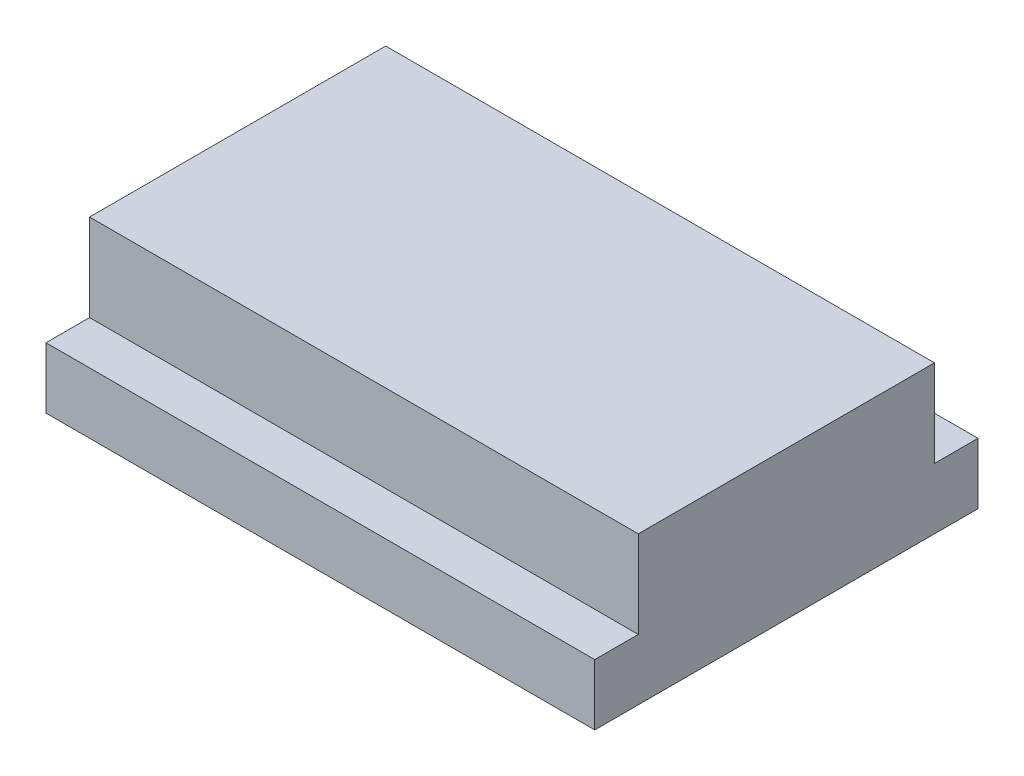
SolidWorks part; units mm, degrees
material "ABS"
ref_plane "Front" through (0, 0, 0) normal (0, 0, 1) x (1, 0, 0)
ref_plane "Top" through (0, 0, 0) normal (0, 1, 0) x (1, 0, 0)
ref_plane "Right" through (0, 0, 0) normal (1, 0, 0) x (0, 0, -1)
sketch "Sketch1" plane through (0, 0, 0) normal (0, 1, 0) x (1, 0, 0)
  line L1 (-31.5, 22) -> (31.5, 22)
  line L2 (-31.5, 22) -> (-31.5, -22)
  line L3 (-31.5, -22) -> (31.5, -22)
  line L4 (31.5, 22) -> (31.5, -22)
  line L5 (-31.5, 22) -> (31.5, -22) construction
  line L6 (-31.5, -22) -> (31.5, 22) construction
  point P0 (0, 0)
  dimension "D1" = 63
  dimension "D2" = 44
extrude "Boss-Extrude1" add sketch "Sketch1" along normal blind 17
sketch "Sketch2" plane through (0, 17, 0) normal (0, 1, 0) x (1, 0, 0)
  line L0 (31.5, -22) -> (31.5, 22) construction
  line L1 (-31.5, 22) -> (31.5, 22)
  line L2 (-31.5, 22) -> (-31.5, 17)
  line L3 (-31.5, 17) -> (31.5, 17)
  line L4 (31.5, 22) -> (31.5, 17)
  line L6 (-31.5, -22) -> (31.5, -22)
  line L7 (-31.5, -22) -> (-31.5, -17)
  line L8 (-31.5, -17) -> (31.5, -17)
  line L9 (31.5, -22) -> (31.5, -17)
  dimension "D1" = 5
extrude "Cut-Extrude1" cut sketch "Sketch2" against normal blind 10
